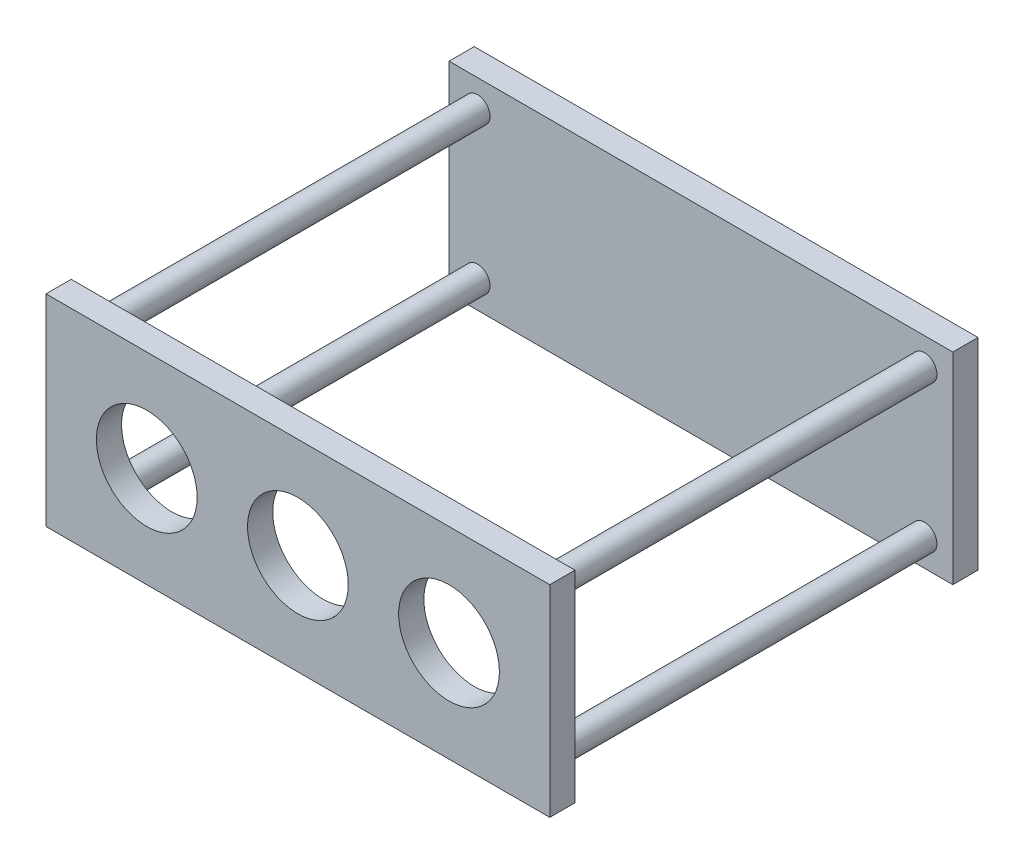
SolidWorks part; units mm, degrees
ref_plane "Front Plane" through (0, 0, 0) normal (0, 0, 1) x (1, 0, 0)
ref_plane "Top Plane" through (0, 0, 0) normal (0, 1, 0) x (1, 0, 0)
ref_plane "Right Plane" through (0, 0, 0) normal (1, 0, 0) x (0, 0, -1)
sketch "Sketch1" plane through (0, 0, 0) normal (0, 0, 1) x (1, 0, 0)
  line L1 (-100, 40) -> (100, 40)
  line L2 (-100, 40) -> (-100, -40)
  line L3 (-100, -40) -> (100, -40)
  line L4 (100, 40) -> (100, -40)
  line L5 (-100, 40) -> (100, -40) construction
  line L6 (-100, -40) -> (100, 40) construction
  point P0 (0, 0)
  point P6 (0, 0)
  point P7 (0, 0)
  dimension "D1" = 80
  dimension "D2" = 200
extrude "Boss-Extrude1" add sketch "Sketch1" along normal blind 10
sketch "Sketch2" plane through (0, 0, 0) normal (0, 0, 1) x (1, 0, 0)
  line L0 (0, 0) -> (0, 32.0189) construction
  line L1 (0, 0) -> (34.6434, 0) construction
  circle A0 centre (-88.7082, 29.132) radius 5
  circle A1 centre (88.7082, 29.132) radius 5
  circle A2 centre (88.7082, -29.132) radius 5
  circle A3 centre (-88.7082, -29.132) radius 5
extrude "Boss-Extrude2" add sketch "Sketch2" along normal blind 160
sketch "Sketch3" plane through (0, 0, 160) normal (0, 0, 1) x (1, 0, 0)
  line L0 (-100, -40) -> (100, -40) construction
  line L1 (-100, 40) -> (100, 40)
  line L2 (-100, 40) -> (-100, -40)
  line L3 (-100, -40) -> (100, -40)
  line L4 (100, 40) -> (100, -40)
extrude "Boss-Extrude3" add sketch "Sketch3" along normal blind 10
sketch "Sketch7" plane through (0, 0, 170) normal (0, 0, 1) x (1, 0, 0)
  circle A0 centre (0, 0) radius 20
  circle A1 centre (-60, 0) radius 20
  circle A2 centre (60, 0) radius 20
  point P16 (-157.2077, -31.2316)
extrude "Cut-Extrude1" cut sketch "Sketch7" against normal blind 10
